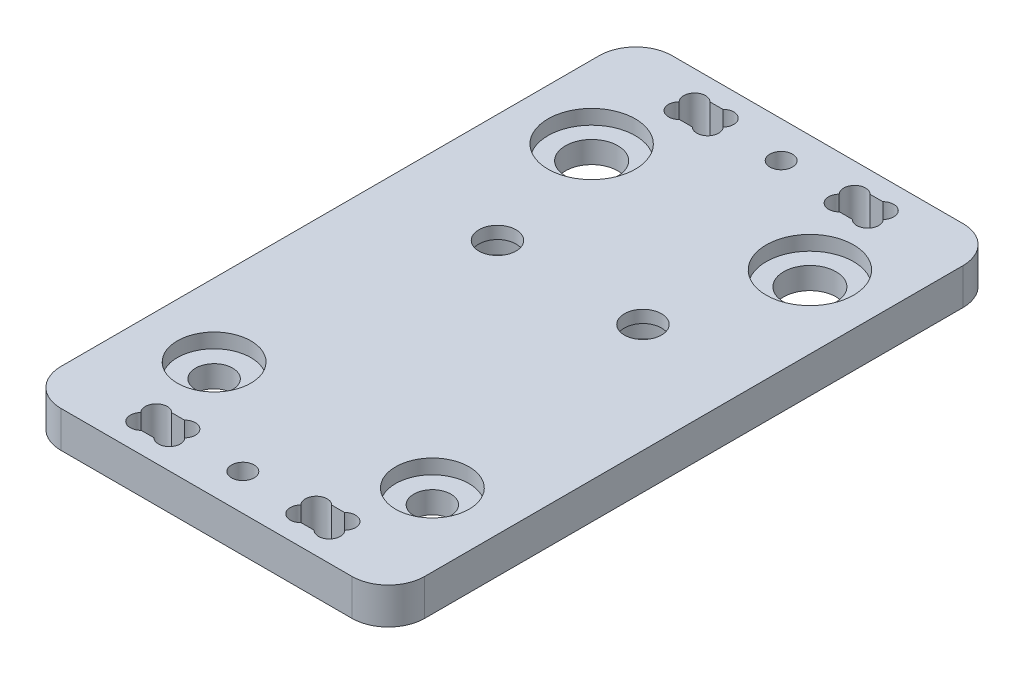
SolidWorks part; units mm, degrees
material "6061-T6 (SS)"
ref_plane "Front Plane" through (0, 0, 0) normal (0, 0, 1) x (1, 0, 0)
ref_plane "Top Plane" through (0, 0, 0) normal (0, 1, 0) x (1, 0, 0)
ref_plane "Right Plane" through (0, 0, 0) normal (1, 0, 0) x (0, 0, -1)
sketch "Sketch1" plane through (0, 0, 0) normal (0, 1, 0) x (1, 0, 0)
  line L0 (-23.7657, 0) -> (0, 0) construction
  line L1 (20.365, -35) -> (-20.365, -35)
  line L2 (25, -30.365) -> (25, 30.365)
  line L3 (20.365, 35) -> (-20.365, 35)
  line L4 (-25, -30.365) -> (-25, 30.365)
  line L5 (25, -35) -> (-25, 35) construction
  line L6 (25, 35) -> (-25, -35) construction
  line L7 (0, 0) -> (0, 28.9978) construction
  arc A0 (-20.365, 35) -> (-25, 30.365) centre (-20.365, 30.365) ccw
  arc A1 (25, 30.365) -> (20.365, 35) centre (20.365, 30.365) ccw
  arc A2 (-20.365, -35) -> (-25, -30.365) centre (-20.365, -30.365) cw
  arc A3 (20.365, -35) -> (25, -30.365) centre (20.365, -30.365) ccw
  circle A4 centre (-15, 25.95) radius 3.6
  circle A16 centre (15, 25.95) radius 3.6
  circle A33 centre (15, -25.95) radius 2.55
  circle A34 centre (-15, -25.95) radius 2.55
  point P0 (0, 0)
  dimension "D2" = 4.635
  dimension "D3" = 30
  dimension "D4" = 7.2
  dimension "D5" = 5.1
  dimension "D6" = 70
  dimension "D7" = 50
  dimension "D10" = 51.9
extrude "Boss-Extrude1" add sketch "Sketch1" along normal blind 5
sketch "Sketch2" plane through (0, 5, 0) normal (0, 1, 0) x (1, 0, 0)
  circle A0 centre (-15, 25.95) radius 6
  circle A1 centre (15, 25.95) radius 6
  circle A2 centre (15, -25.95) radius 5.05
  circle A3 centre (-15, -25.95) radius 5.05
  dimension "D1" = 12
  dimension "D2" = 10.1
extrude "Cut-Extrude1" cut sketch "Sketch2" against normal blind 2
sketch "Croquis3" plane through (0, 5, 0) normal (0, 1, 0) x (1, 0, 0)
  line L0 (-25, 30.365) -> (-25, -30.365) construction
  line L1 (25, -30.365) -> (25, 30.365) construction
  line L2 (-20.365, -35) -> (20.365, -35) construction
  line L3 (0, 0) -> (38.7816, 0) construction
  line L4 (-25, 30.365) -> (-25, 37)
  line L5 (-20, 42) -> (20, 42)
  line L6 (25, 37) -> (25, 30.365)
  line L7 (-20.365, 35) -> (20.365, 35)
  line L8 (-20.365, -35) -> (20.365, -35)
  line L9 (25, -37) -> (25, -30.365)
  line L10 (-20, -42) -> (20, -42)
  line L11 (-25, -30.365) -> (-25, -37)
  arc A0 (-25, -30.365) -> (-20.365, -35) centre (-20.365, -30.365) ccw construction
  arc A1 (20.365, -35) -> (25, -30.365) centre (20.365, -30.365) ccw construction
  arc A2 (25, 30.365) -> (20.365, 35) centre (20.365, 30.365) ccw
  arc A3 (-20.365, 35) -> (-25, 30.365) centre (-20.365, 30.365) ccw
  arc A4 (-25, -37) -> (-20, -42) centre (-20, -37) ccw
  arc A5 (20, -42) -> (25, -37) centre (20, -37) ccw
  arc A6 (-20.365, -35) -> (-25, -30.365) centre (-20.365, -30.365) cw
  arc A7 (25, -30.365) -> (20.365, -35) centre (20.365, -30.365) cw
  arc A8 (20, 42) -> (25, 37) centre (20, 37) cw
  arc A9 (-25, 37) -> (-20, 42) centre (-20, 37) cw
  dimension "D2" = 5
  dimension "D1" = 7
extrude "Saliente-Extruir1" add sketch "Croquis3" against normal up to surface (5 mm away) up to face at (0, 0, 0)
sketch "Croquis5" plane through (0, 0, 0) normal (0, -1, 0) x (1, 0, 0)
  line L0 (-10, -8) -> (10, -8) construction
  line L1 (0, -8) -> (0, 0) construction
  circle A0 centre (10, -8) radius 2.55
  circle A1 centre (-10, -8) radius 2.55
  dimension "D1" = 5.1
  dimension "D2" = 20
  dimension "D3" = 8
extrude "Cortar-Extruir2" cut sketch "Croquis5" against normal through all
sketch "Croquis6" plane through (0, 5, 0) normal (0, 1, 0) x (1, 0, 0)
  line L0 (-30.2461, -34.9) -> (-14, -34.9) construction
  line L1 (-25, -37) -> (-11, -37) construction
  line L2 (-20, -42) -> (20, -42) construction
  line L3 (0, -39.1) -> (0, -34.9) construction
  line L4 (25, -37) -> (11, -37) construction
  line L5 (-25, -39.1) -> (-14, -39.1) construction
  line L6 (-25, -39.1) -> (-25, -34.9) construction
  line L7 (-25, 37) -> (-25, -37) construction
  line L8 (25, -39.1) -> (25, -34.9) construction
  line L9 (25, -37) -> (25, 37) construction
  line L10 (-14, -39.1) -> (-8, -39.1) construction
  line L12 (-8, -34.9) -> (-14, -34.9)
  line L14 (-8, -34.9) -> (29.3675, -34.9) construction
  line L15 (-8, -34.9) -> (-8, -39.1)
  line L16 (-8, -39.1) -> (-14, -39.1)
  line L17 (8, -34.9) -> (14, -34.9)
  line L18 (8, -34.9) -> (8, -39.1)
  line L19 (8, -39.1) -> (14, -39.1)
  line L20 (14, -34.9) -> (14, -39.1)
  line L21 (8, -34.9) -> (14, -39.1) construction
  line L22 (8, -39.1) -> (14, -34.9) construction
  line L27 (-8, -39.1) -> (25, -39.1) construction
  line L29 (-14, -34.9) -> (-14, -39.1)
  line L30 (-8, -34.9) -> (-14, -39.1) construction
  line L31 (-8, -39.1) -> (-14, -34.9) construction
  circle A0 centre (0, -37) radius 1.55
  point P20 (-11, -37)
  point P25 (11, -37)
  dimension "D2" = 3.1
  dimension "D12" = 6
  dimension "D3" = 2.9
  dimension "D5" = 6
  dimension "D6" = 14
  dimension "D13" = 4.2
extrude "Cortar-Extruir3" cut sketch "Croquis6" against normal through all
sketch "Croquis7" plane through (0, 0, 0) normal (0, -1, 0) x (1, 0, 0)
  line L0 (-12.9393, 38.0393) -> (-9.0607, 38.0393) construction
  line L1 (-9.0607, 38.0393) -> (-9.0607, 35.9607) construction
  line L2 (-9.0607, 35.9607) -> (-12.9393, 35.9607) construction
  line L3 (-12.9393, 35.9607) -> (-12.9393, 38.0393) construction
  line L4 (-14, 34.9) -> (-14, 39.1) construction
  line L5 (-14, 39.1) -> (-8, 39.1) construction
  line L6 (-14, 39.1) -> (-12.5, 37.6) construction
  line L7 (-11.8787, 39.1) -> (-10.1213, 39.1)
  line L8 (-11.8787, 34.9) -> (-10.1213, 34.9)
  line L9 (-8, 34.9) -> (-14, 34.9) construction
  line L10 (0, 37) -> (0, 28.6327) construction
  line L11 (11.8787, 34.9) -> (10.1213, 34.9)
  line L12 (11.8787, 39.1) -> (10.1213, 39.1)
  arc A0 (-11.8787, 39.1) -> (-14.0209, 37) centre (-12.9393, 38.0393) ccw
  arc A1 (-7.9791, 37) -> (-10.1213, 39.1) centre (-9.0607, 38.0393) ccw
  arc A2 (-10.1213, 34.9) -> (-7.9791, 37) centre (-9.0607, 35.9607) ccw
  arc A3 (-14.0209, 37) -> (-11.8787, 34.9) centre (-12.9393, 35.9607) ccw
  circle A4 centre (-12.5, 37.6) radius 1.5 construction
  arc A5 (14.0209, 37) -> (11.8787, 34.9) centre (12.9393, 35.9607) cw
  arc A6 (10.1213, 34.9) -> (7.9791, 37) centre (9.0607, 35.9607) cw
  arc A7 (7.9791, 37) -> (10.1213, 39.1) centre (9.0607, 38.0393) cw
  arc A8 (11.8787, 39.1) -> (14.0209, 37) centre (12.9393, 38.0393) cw
  dimension "D1" = 3
extrude "Cortar-Extruir4" cut sketch "Croquis7" against normal through all
sketch "Croquis8" plane through (0, 0, 0) normal (0, -1, 0) x (1, 0, 0)
  circle A0 centre (-10, -8) radius 4.625
  circle A1 centre (10, -8) radius 4.625
  dimension "D1" = 9.25
extrude "Cortar-Extruir5" cut sketch "Croquis8" against normal blind 3.3
sketch "Croquis9" plane through (0, 5, 0) normal (0, 1, 0) x (1, 0, 0)
  line L0 (-25, 37) -> (-25, -37) construction
  line L1 (-20, -42) -> (20, -42) construction
  circle A0 centre (-21, -11.48) radius 2.575
  dimension "D3" = 5.15
  dimension "D1" = 4
  dimension "D2" = 30.52
extrude "Cortar-Extruir6" [suppressed] cut sketch "Croquis9" against normal through all
mirror "Simetría1" about plane through (0, 0, 0) normal (0, 0, 1) of "Cortar-Extruir3", "Cortar-Extruir4"
